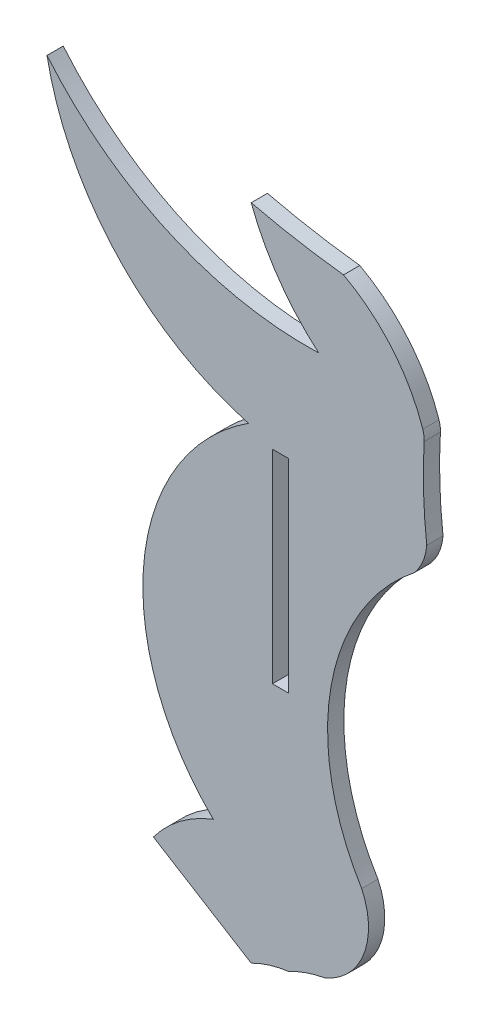
SolidWorks part; units mm, degrees
ref_plane "Front Plane" through (0, 0, 0) normal (0, 0, 1) x (1, 0, 0)
ref_plane "Top Plane" through (0, 0, 0) normal (0, 1, 0) x (1, 0, 0)
ref_plane "Right Plane" through (0, 0, 0) normal (1, 0, 0) x (0, 0, -1)
sketch "Sketch1" plane through (0, 0, 0) normal (0, 0, 1) x (1, 0, 0)
  line L1 (1.524, -174.0497) -> (0, -174.0497)
  line L2 (1.524, -174.0497) -> (1.524, -193.0997)
  line L3 (1.524, -193.0997) -> (0, -193.0997)
  line L4 (0, -174.0497) -> (0, -193.0997)
  line L5 (-11.1636, -211.1209) -> (-1.9929, -216.7806)
  arc A0 (-2.2542, -173.0728) -> (-21.1398, -152.6415) centre (4.7413, -147.6625) cw
  arc A1 (-21.1398, -152.6415) -> (4.3305, -164.0609) centre (3.2342, -132.3914) ccw
  arc A2 (4.3305, -164.0609) -> (-1.9929, -155.0302) centre (18.778, -147.2151) cw
  arc A3 (-1.9929, -155.0302) -> (6.6646, -156.5606) centre (15.1562, -83.2694) ccw
  arc A4 (6.6646, -156.5606) -> (14.0945, -165.3776) centre (-0.7957, -170.3862) cw
  arc A5 (14.2232, -166.3279) -> (14.4684, -174.622) centre (63.0676, -169.0343) ccw
  arc A6 (14.4684, -174.622) -> (13.3114, -177.4142) centre (9.5528, -174.221) cw
  arc A7 (13.3114, -177.4142) -> (8.3663, -205.5458) centre (26.6767, -194.2641) ccw
  arc A8 (8.3663, -205.5458) -> (4.9113, -214.5273) centre (2.372, -208.3952) cw
  arc A9 (4.9113, -214.5273) -> (1.524, -215.7006) centre (6.9154, -225.7894) ccw
  arc A10 (-1.9929, -216.7806) -> (1.524, -215.7006) centre (2.8691, -226.3471) cw
  arc A12 (14.2232, -166.3279) -> (14.0945, -165.3776) centre (11.687, -166.1874) ccw
  arc A14 (-2.2542, -173.0728) -> (-5.5486, -206.8745) centre (9.5545, -191.2851) ccw
  arc A15 (-5.5486, -206.8745) -> (-11.1636, -211.1209) centre (-1.0563, -218.6503) ccw
  ellipse E0 centre (4.6149, -132.9386) end of major axis (28.0799, -111.6224) minor radius 30.6532 (-21.801, -150.419) -> (3.8945, -164.0684) ccw construction
extrude "Boss-Extrude1" add sketch "Sketch1" along normal blind 1.524
